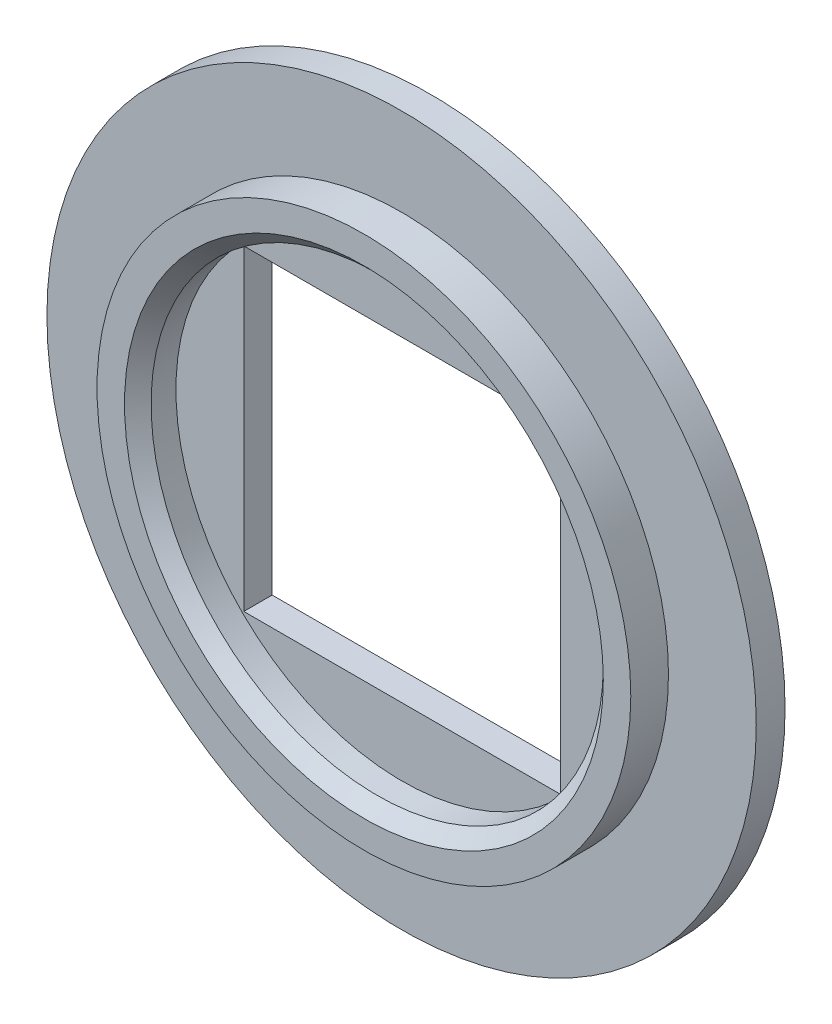
SolidWorks part; units mm, degrees
ref_plane "前视基准面" through (0, 0, 0) normal (0, 0, 1) x (1, 0, 0)
ref_plane "上视基准面" through (0, 0, 0) normal (0, 1, 0) x (1, 0, 0)
ref_plane "右视基准面" through (0, 0, 0) normal (1, 0, 0) x (0, 0, -1)
sketch "草图1" plane through (0, 0, 0) normal (0, 0, 1) x (1, 0, 0)
  circle A0 centre (0, 0) radius 8
extrude "凸台-拉伸1" add sketch "草图1" along normal blind 0.65
sketch "草图2" plane through (0, 0, 0) normal (0, 0, 1) x (1, 0, 0)
  circle A0 centre (0, 0) radius 6.02
  circle A1 centre (0, 0) radius 5.1
extrude "凸台-拉伸2" add sketch "草图2" along normal blind 0.85 from surface at 0.65 starting at face at (8, 0, 0.65)
sketch "草图3" plane through (0, 0, 0) normal (0, 0, 1) x (1, 0, 0)
  circle A0 centre (0, 0) radius 5.1
extrude "切除-拉伸1" cut sketch "草图3" against normal blind 0.01 from surface at 0.65 starting at face at (6.02, 0, 0.65)
sketch "草图4" plane through (0, 0, 0) normal (0, 0, 1) x (1, 0, 0)
  line L16 (-3.57, 3.57) -> (3.57, 3.57)
  line L17 (-3.57, 0) -> (-3.57, 3.57)
  line L18 (-3.57, 0) -> (-3.57, -3.57)
  line L19 (-3.57, -3.57) -> (3.57, -3.57)
  line L20 (3.57, 3.57) -> (3.57, -3.57)
extrude "切除-拉伸2" cut sketch "草图4" along normal up to surface (0.64 mm away) up to face at (5.1, 0, 0.64)
chamfer "倒角1" distance 0.3 angle 45 1 edges at (5.1, 0, 1.5)
